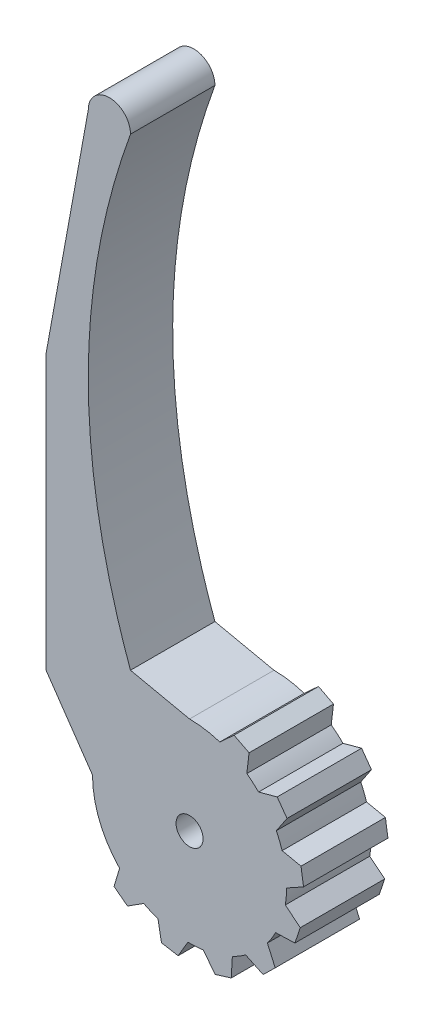
SolidWorks part; units mm, degrees
ref_plane "前基準面" through (0, 0, 0) normal (0, 0, 1) x (1, 0, 0)
ref_plane "上基準面" through (0, 0, 0) normal (0, 1, 0) x (1, 0, 0)
ref_plane "右基準面" through (0, 0, 0) normal (1, 0, 0) x (0, 0, -1)
sketch "草圖1" plane through (0, 0, 0) normal (0, 0, 1) x (1, 0, 0)
  line L0 (0, 0) -> (0, 55) construction
  line L1 (0, 27.5) -> (-5, 27.5) construction
  line L2 (0, 55) -> (-5, 55) construction
  line L3 (-5, 27.5) -> (-10, 27.5) construction
  line L4 (-5, 55) -> (-10, 27.5)
  line L5 (-10, 27.5) -> (-10, -5)
  line L6 (0, 0) -> (0, -13) construction
  line L7 (0, -13) -> (7, -13) construction
  line L8 (-10, -5) -> (-4.5, -13)
  line L9 (0, 0) -> (7, -1.5)
  line L10 (7, -13) -> (7, -1.5) construction
  line L11 (7, -13) -> (10.5804, -2.0716) construction
  line L12 (7, -13) -> (13.7822, -3.7128) construction
  line L13 (10.5804, -2.0716) -> (13.7822, -3.7128) construction
  line L14 (10.5804, -2.0716) -> (12.2684, -0.5303)
  line L15 (12.2684, -0.5303) -> (14.0481, -1.4426)
  line L16 (14.0481, -1.4426) -> (13.7822, -3.7128)
  line L17 (15.1718, -4.9085) -> (17.377, -4.307)
  line L18 (17.377, -4.307) -> (18.5446, -5.9308)
  line L19 (18.5446, -5.9308) -> (17.2722, -7.8298)
  line L20 (17.9633, -9.5277) -> (20.2, -9.9984)
  line L21 (20.2, -9.9984) -> (20.4982, -11.9761)
  line L22 (20.4982, -11.9761) -> (18.4997, -13.0854)
  line L23 (18.34, -14.9116) -> (20.1157, -16.351)
  line L24 (20.1157, -16.351) -> (19.4788, -18.2469)
  line L25 (19.4788, -18.2469) -> (17.1943, -18.3223)
  line L26 (16.219, -19.8745) -> (17.1425, -21.9655)
  line L27 (17.1425, -21.9655) -> (15.7108, -23.362)
  line L28 (15.7108, -23.362) -> (13.6435, -22.3869)
  line L29 (12.0675, -23.3233) -> (11.9354, -25.6052)
  line L30 (11.9354, -25.6052) -> (10.0243, -26.1948)
  line L31 (10.0243, -26.1948) -> (8.6294, -24.384)
  line L32 (6.7999, -24.4983) -> (5.6412, -26.4686)
  line L33 (5.6412, -26.4686) -> (3.6716, -26.1214)
  line L34 (3.6716, -26.1214) -> (3.2565, -23.8737)
  line L35 (1.5763, -23.1407) -> (-0.3537, -24.3655)
  line L36 (-0.3537, -24.3655) -> (-1.948, -23.1579)
  line L37 (-1.948, -23.1579) -> (-1.2919, -20.9683)
  arc A0 (-5, 55) -> (0, 55) centre (-2.5, 55) cw
  circle A1 centre (7, -13) radius 11.5
  spline S0 degree 2 poles (0, 55) (-10, 27.5) (0, 0) knots 0 0 0 1 1 1
  dimension "D6" = 13
  dimension "D8" = 23
  dimension "D1" = 55
  dimension "D2" = 5
  dimension "D3" = 5
  dimension "D4" = 5
  dimension "D5" = 5
  dimension "D7" = 7
  dimension "D9" = 18.14
  dimension "D10" = 18
  dimension "D11" = 13.5
  dimension "D12" = 2
  dimension "D13" = 8
extrude "填料-伸長2" add sketch "草圖1" along normal blind 10 contours A1 | A1 L22 L21 L20 | A1 L19 L18 L17 | A1 L16 L15 L14 | A1 L25 L24 L23 | A1 L28 L27 L26 | A1 L31 L30 L29 | A1 L34 L33 L32 | A1 L37 L36 L35 | S0 A0 L4 L5 L8 A1 L9
sketch "草圖2" plane through (0, 0, 0) normal (0, 0, -1) x (-1, 0, 0)
  circle A0 centre (-7, -13) radius 1.6
  arc A3 (1.2919, -20.9683) -> (4.5, -13) centre (-7, -13) ccw construction
  dimension "D1" = 3.2
extrude "除料-伸長1" cut sketch "草圖2" against normal blind 10
